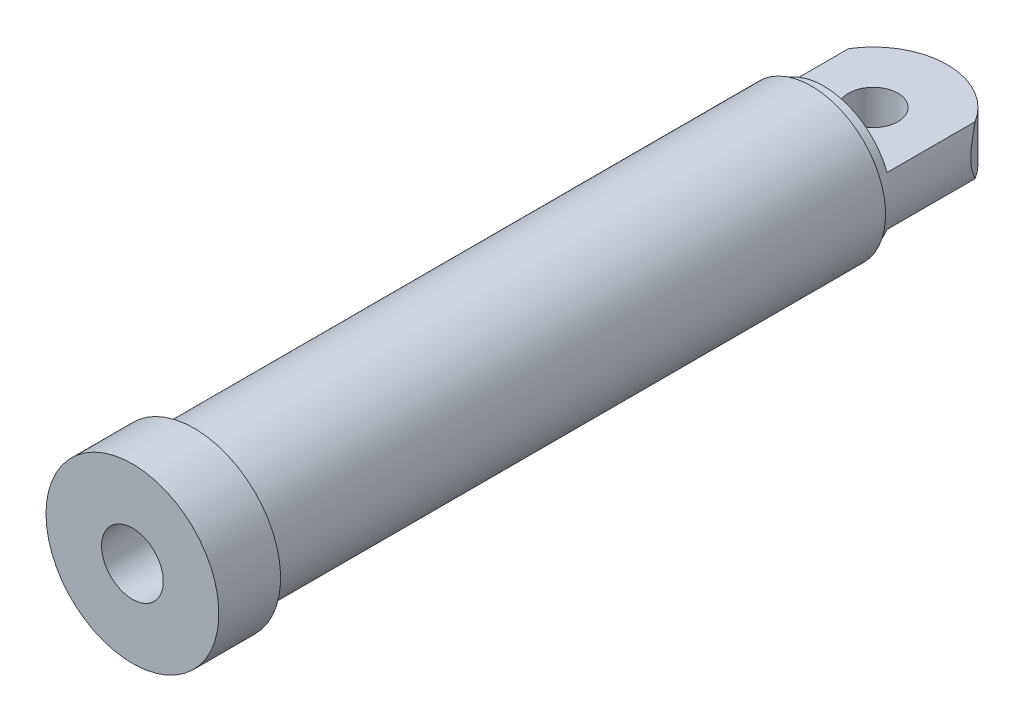
SolidWorks part; units mm, degrees
material "AISI 4340 Steel, normalized"
ref_plane "Front Plane" through (0, 0, 0) normal (0, 0, 1) x (1, 0, 0)
ref_plane "Top Plane" through (0, 0, 0) normal (0, 1, 0) x (1, 0, 0)
ref_plane "Right Plane" through (0, 0, 0) normal (1, 0, 0) x (0, 0, -1)
sketch "Sketch1" plane through (0, 0, 0) normal (0, 1, 0) x (1, 0, 0)
  line L0 (0, 0) -> (0, -600) construction
  line L1 (0, -600) -> (70, -600) construction
  line L2 (70, -600) -> (70, -550)
  line L3 (70, -550) -> (60, -550)
  line L4 (60, -550) -> (60, -40)
  line L5 (60, -40) -> (0, -40)
  line L6 (70, -600) -> (25, -600)
  line L7 (25, -600) -> (25, -520)
  line L8 (25, -520) -> (45, -520)
  line L9 (45, -520) -> (45, -60)
  line L10 (45, -60) -> (0, -60)
  line L11 (0, -60) -> (0, -40)
  circle A0 centre (0, 0) radius 20 construction
  circle A1 centre (0, 0) radius 60 construction
  dimension "D5" = 120
  dimension "D6" = 40
  dimension "D1" = 600
  dimension "D2" = 120
  dimension "D3" = 10
  dimension "D4" = 50
  dimension "D7" = 80
  dimension "D8" = 15
  dimension "D9" = 50
  dimension "D10" = 20
  dimension "D11" = 40
revolve "Revolve1" add sketch "Sketch1" angle 360 about L0
sketch "Sketch2" plane through (0, 0, 0) normal (0, 1, 0) x (1, 0, 0)
  line L0 (60, -40) -> (60, 0)
  line L1 (-60, -40) -> (-60, 0)
  line L2 (60, -40) -> (-60, -40)
  circle A0 centre (0, 0) radius 20
  circle A1 centre (0, 0) radius 20 construction
  arc A2 (60, 0) -> (-60, 0) centre (0, 0) ccw
  circle A3 centre (0, 0) radius 60 construction
extrude "Boss-Extrude1" add sketch "Sketch2" along normal mid plane 40
sketch "Sketch3" plane through (0, 0, 40) normal (0, 0, -1) x (-1, 0, 0)
  circle A0 centre (0, 0) radius 55
  circle A2 centre (0, 0) radius 63.2456
  arc A3 (56.5685, 20) -> (-56.5685, 20) centre (0, 0) ccw construction
  dimension "D1" = 5
extrude "Cut-Extrude1" cut sketch "Sketch3" along normal through all and the other way blind 10
